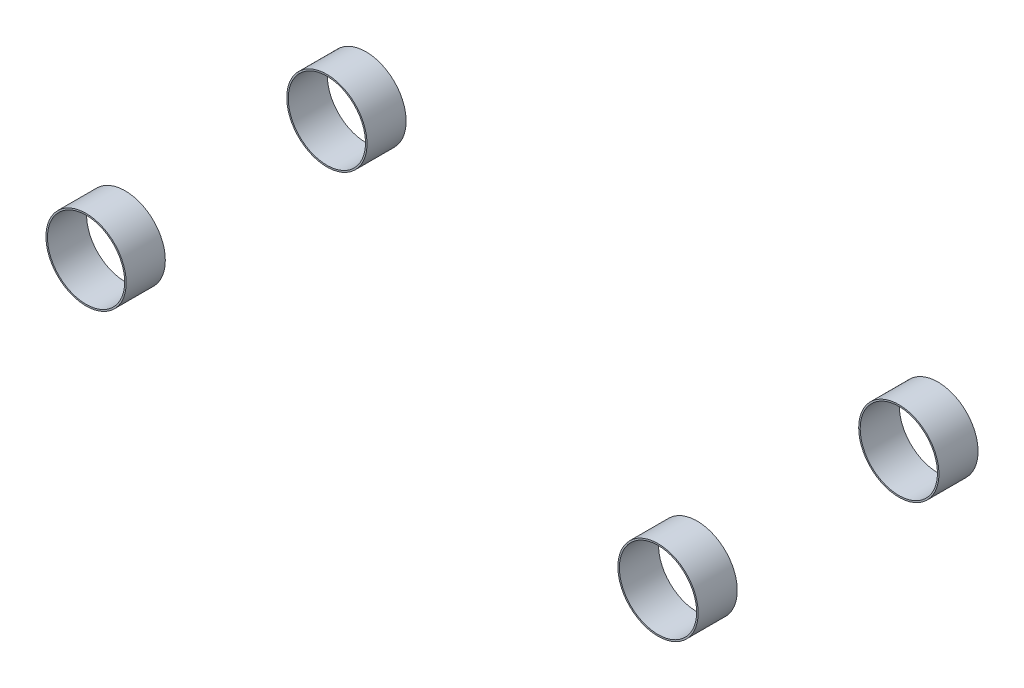
SolidWorks part; units mm, degrees
ref_plane "Front Plane" through (0, 0, 0) normal (0, 0, 1) x (1, 0, 0)
ref_plane "Top Plane" through (0, 0, 0) normal (0, 1, 0) x (1, 0, 0)
ref_plane "Right Plane" through (0, 0, 0) normal (1, 0, 0) x (0, 0, -1)
sketch "Sketch2" plane through (0, 0, 0) normal (0, 1, 0) x (1, 0, 0)
  line L0 (-1425, 600) -> (1425, 600)
  line L1 (-1425, 600) -> (-1425, -600)
  line L2 (-1425, -600) -> (1425, -600)
  line L3 (1425, 600) -> (1425, -600)
  point P0 (0, 0)
  point P5 (0, 0)
  point P6 (0, 0)
ref_plane "left" through (0, 0, 600) normal (0, 0, 1) x (1, 0, 0)
ref_plane "right" through (0, 0, -600) normal (0, 0, -1) x (-1, 0, 0)
sketch "Sketch3" plane through (0, 0, 600) normal (0, 0, 1) x (1, 0, 0)
  line L0 (-1425, 0) -> (1425, 0) construction
  line L1 (-1425, 0) -> (1425, 0) construction
  circle A0 centre (-1425, 0) radius 200
  circle A1 centre (1425, 0) radius 200
  circle A2 centre (-1425, 0) radius 192.5
  circle A3 centre (1425, 0) radius 192.5
extrude "Boss-Extrude1" add sketch "Sketch3" along normal mid plane 195
sketch "Sketch5" plane through (0, 0, -600) normal (0, 0, -1) x (-1, 0, 0)
  circle A0 centre (-1425, 0) radius 200
  circle A1 centre (-1425, 0) radius 192.5
  circle A2 centre (1425, 0) radius 200
  circle A3 centre (1425, 0) radius 192.5
extrude "Boss-Extrude2" add sketch "Sketch5" along normal mid plane 195 separate body
ref_plane "front" through (1425, 0, 0) normal (1, 0, 0) x (0, 0, -1)
ref_plane "rear" through (-1425, 0, 0) normal (-1, 0, 0) x (0, 0, 1)
sketch "Sketch6" plane through (-1425, 0, 0) normal (-1, 0, 0) x (0, 0, 1)
  line L0 (-550, -828.3251) -> (-550, 49171.6749) construction
  line L1 (550, -954.3859) -> (550, 49045.6141) construction
  line L2 (-600, 220) -> (-600, -220) construction
  line L3 (600, -220) -> (600, 220) construction
  line L4 (-1209.8249, -75) -> (48790.1751, -75) construction
  line L5 (-1199.8727, 175) -> (48800.1273, 175) construction
  line L6 (-697.5, -200) -> (-502.5, -200) construction
  line L7 (-552.7656, 175) -> (380.2471, -75) construction
  line L8 (550, 175) -> (-383.0127, -75) construction
  line L9 (-600, -200) -> (380.2471, -75) construction
  line L10 (600, -200) -> (-383.0127, -75) construction
  point P14 (-600, -200)
  point P15 (600, -200)
  point P18 (-0.8452, -123.5965)
  point P20 (0, 0)
  point P22 (0, 0)
  point P23 (0, 0)
  point P26 (0, 0)
  point P27 (0, 0)
  dimension "D1" = 50
  dimension "D2" = 50
  dimension "D3" = 125
  dimension "D4" = 375
  dimension "D5" = 15
  dimension "D6" = 15
  dimension "D7" = 76.4035
ref_plane "Left WB" through (0, 0, 550) normal (0, 0, 1) x (1, 0, 0)
sketch "Sketch9" plane through (0, 0, 550) normal (0, 0, 1) x (1, 0, 0)
  line L0 (-1425, 175) -> (353.8424, -75) construction
  line L1 (-1425, -200954.3859) -> (-1425, 249045.6141) construction
  line L2 (0, 1504.8134) -> (0, -1504.8134) construction
  line L4 (353.8424, -75) -> (-1425, -200) construction
  line L5 (-353.8424, -75) -> (1425, -200) construction
  line L6 (1425, 175) -> (-353.8424, -75) construction
  line L8 (-1425, -75) -> (1425, -75) construction
  line L9 (-1425, 175) -> (-1425, -75) construction
  line L10 (-1425, -200) -> (-1425, -75) construction
  line L11 (1425, -220) -> (1425, 220) construction
  point P16 (0, -99.8647)
  point P22 (0, 0)
  dimension "D1" = 8
  dimension "D2" = 100.1353
